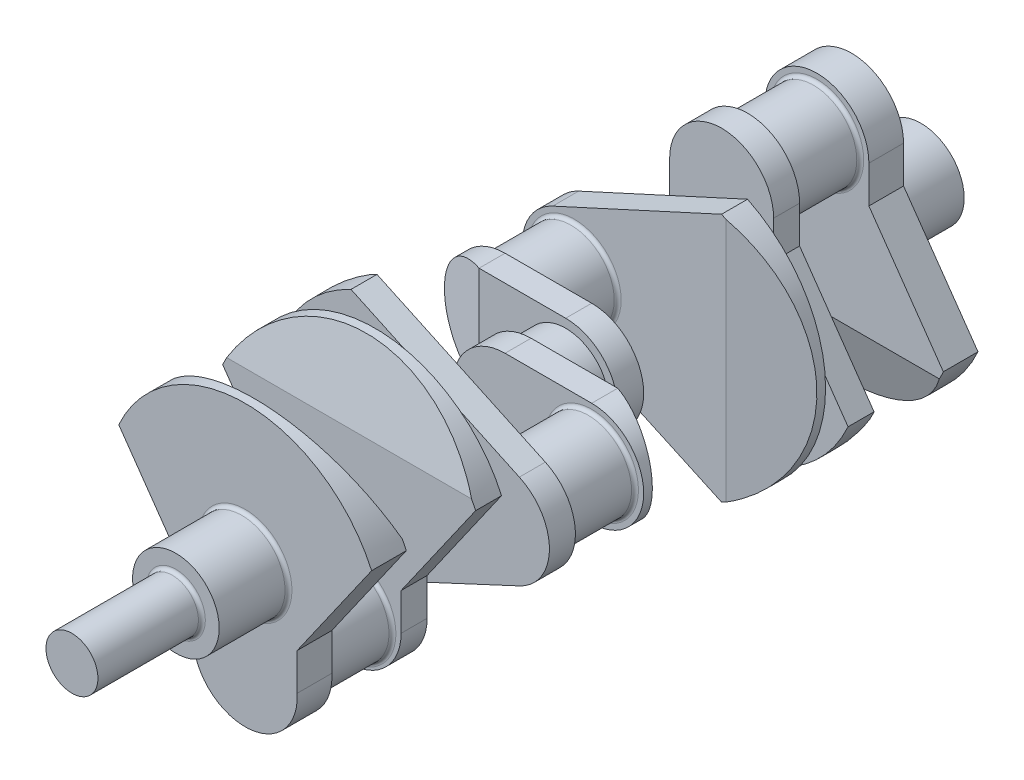
SolidWorks part; units mm, degrees
material "AISI 4340 Steel, normalized"
ref_plane "Front Plane" through (0, 0, 0) normal (0, 0, 1) x (1, 0, 0)
ref_plane "Top Plane" through (0, 0, 0) normal (0, 1, 0) x (1, 0, 0)
ref_plane "Right Plane" through (0, 0, 0) normal (1, 0, 0) x (0, 0, -1)
sketch "Sketch1" plane through (0, 0, 0) normal (0, 0, 1) x (1, 0, 0)
  circle A0 centre (0, 0) radius 31.75
  dimension "D1" = 63.5
extrude "Boss-Extrude1" add sketch "Sketch1" along normal blind 50.8
sketch "Sketch2" plane through (0, 0, 50.8) normal (0, 0, 1) x (1, 0, 0)
  line L0 (-38.1, 63.5) -> (-38.1, 36.322)
  line L1 (-38.1, 36.322) -> (-92.6807, -41.6274)
  line L2 (0, 115.8305) -> (0, -116.946) construction
  line L3 (38.1, 36.322) -> (92.6807, -41.6274)
  line L4 (38.1, 63.5) -> (38.1, 36.322)
  arc A0 (38.1, 63.5) -> (-38.1, 63.5) centre (0, 63.5) ccw
  arc A1 (-92.6807, -41.6274) -> (92.6807, -41.6274) centre (0, 0) ccw
  point P1 (38.1, 35.7985)
  point P3 (101.6, 0)
  point P13 (-92.7564, -41.4585)
  dimension "D1" = 203.2
  dimension "D3" = 38.1
  dimension "D2" = 63.5
  dimension "D4" = 27.178
  dimension "D5" = 145
extrude "Boss-Extrude2" add sketch "Sketch2" along normal blind 25.4
sketch "Sketch3" plane through (0, 0, 76.2) normal (0, 0, 1) x (1, 0, 0)
  circle A0 centre (0, 63.5) radius 31.75
  dimension "D1" = 63.5
extrude "Boss-Extrude3" add sketch "Sketch3" along normal blind 50.8
sketch "Sketch4" plane through (0, 0, 127) normal (0, 0, 1) x (1, 0, 0)
  line L0 (-38.1, 63.5) -> (-38.1, 36.322)
  line L1 (-38.1, 36.322) -> (-92.6807, -41.6274)
  line L2 (38.1, 63.5) -> (38.1, 36.322)
  line L3 (38.1, 36.322) -> (92.6807, -41.6274)
  line L4 (92.6807, -41.6274) -> (38.1, 36.322) construction
  arc A0 (38.1, 63.5) -> (-38.1, 63.5) centre (0, 63.5) ccw
  arc A1 (-92.6807, -41.6274) -> (92.6807, -41.6274) centre (0, 0) ccw
  point P1 (101.6, 0)
  point P4 (92.6807, -41.6274)
extrude "Boss-Extrude4" add sketch "Sketch4" along normal blind 19.05
sketch "Sketch5" plane through (0, 0, 146.05) normal (0, 0, 1) x (1, 0, 0)
  circle A0 centre (0, 0) radius 31.75
  dimension "D1" = 63.5
extrude "Boss-Extrude5" add sketch "Sketch5" along normal blind 25.4
sketch "Sketch6" plane through (0, 0, 171.45) normal (0, 0, 1) x (1, 0, 0)
  line L0 (-79.3697, 34.6761) -> (44.4018, 91.384)
  line L1 (44.4307, -91.37) -> (-79.322, -34.6209)
  arc A1 (-79.3697, 34.6761) -> (-79.322, -34.6209) centre (-63.5, 0.0385) ccw
  arc A2 (44.4307, -91.37) -> (44.4018, 91.384) centre (0, 0) ccw
  dimension "D1" = 63.5
  dimension "D2" = 38.1
  dimension "D3" = 101.6
  dimension "D4" = 136.144
extrude "Boss-Extrude6" add sketch "Sketch6" along normal blind 19.05
sketch "Sketch7" plane through (0, 0, 190.5) normal (0, 0, 1) x (1, 0, 0)
  circle A0 centre (-63.5, 0.0385) radius 31.75
  dimension "D1" = 63.5
extrude "Boss-Extrude7" add sketch "Sketch7" along normal blind 50.8
sketch "Sketch8" plane through (0, 0, 241.3) normal (0, 0, 1) x (1, 0, 0)
  line L0 (-63.5, 0) -> (0, 0) construction
  line L1 (-63.5, 38.1) -> (0, 38.1)
  line L2 (-63.5, -38.1) -> (0, -38.1)
  arc A0 (-63.5, 38.1) -> (-63.5, -38.1) centre (-63.5, 0) ccw
  arc A1 (0, -38.1) -> (0, 38.1) centre (0, 0) ccw
  point P4 (-31.75, 0)
  dimension "D1" = 38.1
extrude "Boss-Extrude8" add sketch "Sketch8" along normal blind 19.05
sketch "Sketch9" plane through (0, 0, 260.35) normal (0, 0, 1) x (1, 0, 0)
  circle A0 centre (0, 0) radius 31.75
  dimension "D1" = 63.5
extrude "Boss-Extrude9" add sketch "Sketch9" along normal blind 25.4
sketch "Sketch10" plane through (0, 0, 285.75) normal (0, 0, 1) x (1, 0, 0)
  line L0 (0, 0) -> (63.5, 0) construction
  line L1 (0, 38.1) -> (63.5, 38.1)
  line L2 (0, -38.1) -> (63.5, -38.1)
  arc A0 (0, 38.1) -> (0, -38.1) centre (0, 0) ccw
  arc A1 (63.5, -38.1) -> (63.5, 38.1) centre (63.5, 0) ccw
  point P4 (31.75, 0)
  dimension "D1" = 38.1
  dimension "D2" = 63.5
extrude "Boss-Extrude10" add sketch "Sketch10" along normal blind 19.05
sketch "Sketch11" plane through (0, 0, 304.8) normal (0, 0, 1) x (1, 0, 0)
  circle A0 centre (63.5, 0) radius 31.75
  dimension "D1" = 63.5
extrude "Boss-Extrude11" add sketch "Sketch11" along normal blind 50.8
sketch "Sketch12" plane through (0, 0, 355.6) normal (0, 0, 1) x (1, 0, 0)
  line L0 (-43.0921, 92.0088) -> (80.3275, 34.5391)
  line L1 (-43.0921, -92.0088) -> (80.3275, -34.5391)
  arc A0 (-43.0921, 92.0088) -> (-43.0921, -92.0088) centre (0, 0) ccw
  arc A1 (80.3275, -34.5391) -> (80.3275, 34.5391) centre (64.2446, 0) ccw
  point P1 (0, 101.6)
  point P4 (-50.2595, 88.298)
  point P7 (-37.9177, 94.2592)
  point P10 (3.2398, 101.462)
  point P12 (44.4307, -91.37)
  point P13 (-43.5194, -91.8075)
  point P14 (-7.4828, 96.0044)
  point P15 (3.2398, 101.462)
  point P16 (-43.0921, 92.0088)
  dimension "D1" = 38.1
  dimension "D3" = 101.6
  dimension "D2" = 136.144
extrude "Boss-Extrude12" add sketch "Sketch12" along normal blind 19.05
sketch "Sketch13" plane through (0, 0, 374.65) normal (0, 0, 1) x (1, 0, 0)
  circle A0 centre (0, 0) radius 31.75
  dimension "D1" = 63.5
extrude "Boss-Extrude13" add sketch "Sketch13" along normal blind 25.4
sketch "Sketch15" plane through (0, 0, 400.05) normal (0, 0, 1) x (1, 0, 0)
  line L0 (-38.1, -63.5) -> (-38.1, -36.322)
  line L1 (-38.1, -36.322) -> (-92.6807, 41.6274)
  line L2 (0, 94.3419) -> (0, -122.7433) construction
  line L3 (38.1, -63.5) -> (38.1, -36.322)
  line L4 (38.1, -36.322) -> (92.6807, 41.6274)
  arc A0 (-38.1, -63.5) -> (38.1, -63.5) centre (0, -63.5) ccw
  arc A2 (92.6807, 41.6274) -> (-92.6807, 41.6274) centre (0, 0) ccw
  point P1 (-38.1, -27.8487)
  point P3 (0, 0)
  point P13 (-63.5, 0)
  point P14 (-60.0415, -20.6704)
  point P15 (-60.0415, -20.6704)
  point P16 (-63.1756, 6.4107)
  dimension "D1" = 63.5
  dimension "D2" = 27.178
  dimension "D3" = 76.2
  dimension "D4" = 101.6
  dimension "D5" = 145
extrude "Boss-Extrude14" add sketch "Sketch15" along normal blind 19.05
sketch "Sketch16" plane through (0, 0, 419.1) normal (0, 0, 1) x (1, 0, 0)
  circle A0 centre (0, -65.6946) radius 31.75
  dimension "D1" = 63.5
extrude "Boss-Extrude15" add sketch "Sketch16" along normal blind 50.8
sketch "Sketch17" plane through (0, 0, 469.9) normal (0, 0, 1) x (1, 0, 0)
  line L0 (-92.6807, 41.6274) -> (-38.1, -36.322)
  line L1 (-38.1, -36.322) -> (-38.1, -63.5)
  line L2 (0, 109.8707) -> (0, -120.37) construction
  line L3 (38.1, -36.322) -> (38.1, -63.5)
  line L4 (92.6807, 41.6274) -> (38.1, -36.322)
  arc A2 (-38.1, -63.5) -> (38.1, -63.5) centre (0, -65.6946) ccw
  arc A3 (92.6807, 41.6274) -> (-92.6807, 41.6274) centre (0, 0) ccw
  point P1 (-101.6, 0)
  point P4 (-92.6807, 41.6274)
  dimension "D1" = 101.6
extrude "Boss-Extrude16" add sketch "Sketch17" along normal blind 25.4
sketch "Sketch18" plane through (0, 0, 495.3) normal (0, 0, 1) x (1, 0, 0)
  circle A0 centre (0, 0) radius 31.75
  dimension "D1" = 63.5
extrude "Boss-Extrude17" add sketch "Sketch18" along normal blind 50.8
sketch "Sketch19" plane through (0, 0, 546.1) normal (0, 0, 1) x (1, 0, 0)
  circle A0 centre (0, 0) radius 19.05
  dimension "D1" = 38.1
extrude "Boss-Extrude18" add sketch "Sketch19" along normal blind 76.2
fillet "Fillet1" radius 2.54 16 edges at (31.75, 0, 50.8) (31.75, 63.5, 127) (31.75, 0, 146.05) (31.75, 63.5, 76.2) (-31.75, 0.0385, 190.5) (31.75, 0, 171.45) (31.75, 0, 285.75) (-31.75, 0.0385, 241.3) (31.75, 0, 400.05) (95.25, 0, 304.8) (31.75, 0, 374.65) (95.25, 0, 355.6) (31.75, -65.6946, 419.1) (31.75, -65.6946, 469.9) (31.75, 0, 495.3) (19.05, 0, 546.1)
sketch "Sketch20" plane through (0, 0, 0) normal (1, 0, 0) x (0, 0, -1)
  line L0 (-488.95, 101.6) -> (-469.9, 47.625)
  line L1 (-469.9, 101.6) -> (-495.3, 101.6) construction
  line L2 (-469.9, 41.6274) -> (-469.9, 101.6) construction
  line L3 (-469.9, 47.625) -> (-469.9, 101.6)
  line L4 (-469.9, 101.6) -> (-488.95, 101.6)
  line L5 (-419.1, 47.625) -> (-419.1, 101.6)
  line L6 (-419.1, 101.6) -> (-419.1, 41.6274) construction
  line L7 (-419.1, 101.6) -> (-406.4, 101.6)
  line L8 (-400.05, 101.6) -> (-419.1, 101.6) construction
  line L9 (-406.4, 101.6) -> (-419.1, 47.625)
  line L10 (-139.7, -101.6) -> (-127, -101.6)
  line L11 (-146.05, -101.6) -> (-127, -101.6) construction
  line L12 (-127, -101.6) -> (-127, -47.625)
  line L13 (-127, -101.6) -> (-127, -41.6274) construction
  line L14 (-127, -47.625) -> (-139.7, -101.6)
  line L15 (-57.15, -101.6) -> (-76.2, -101.6)
  line L16 (-76.2, -101.6) -> (-76.2, -47.625)
  line L17 (-76.2, -41.6274) -> (-76.2, -101.6) construction
  line L18 (-76.2, -47.625) -> (-57.15, -101.6)
  dimension "D1" = 19.05
  dimension "D2" = 12.7
  dimension "D3" = 53.975
  dimension "D4" = 53.975
  dimension "D5" = 53.975
  dimension "D6" = 12.7
  dimension "D7" = 19.05
  dimension "D8" = 53.975
extrude "Cut-Extrude1" cut sketch "Sketch20" against normal mid plane 277.114
sketch "Sketch21" plane through (0, 0, 0) normal (0, 1, 0) x (1, 0, 0)
  line L0 (101.6, -177.8) -> (101.6, -190.5)
  line L1 (101.6, -190.5) -> (101.6, -171.45) construction
  line L2 (101.6, -190.5) -> (47.625, -190.5)
  line L3 (44.4018, -190.5) -> (101.6, -190.5) construction
  line L4 (47.625, -190.5) -> (101.6, -177.8)
  line L5 (-101.6, -247.65) -> (-101.6, -260.35)
  line L6 (-101.6, -241.3) -> (-101.6, -260.35) construction
  line L7 (-101.6, -260.35) -> (-63.5, -260.35)
  line L8 (0, -260.35) -> (-63.5, -260.35) construction
  line L9 (-63.5, -260.35) -> (-101.6, -247.65)
  line L10 (63.5, -285.75) -> (101.6, -285.75)
  line L11 (101.6, -285.75) -> (63.5, -285.75) construction
  line L12 (101.6, -285.75) -> (101.6, -298.45)
  line L13 (101.6, -304.8) -> (101.6, -285.75) construction
  line L14 (101.6, -298.45) -> (63.5, -285.75)
  line L15 (63.5, -304.8) -> (63.5, -285.75) construction
  line L16 (-101.6, -355.6) -> (-101.6, -368.3)
  line L17 (-101.6, -355.6) -> (-101.6, -374.65) construction
  line L18 (-101.6, -368.3) -> (-47.625, -355.6)
  line L19 (-43.0921, -355.6) -> (-101.6, -355.6) construction
  line L20 (-47.625, -355.6) -> (-101.6, -355.6)
  dimension "D1" = 53.975
  dimension "D2" = 12.7
  dimension "D3" = 12.7
  dimension "D4" = 12.7
  dimension "D5" = 53.975
  dimension "D6" = 12.7
extrude "Cut-Extrude2" cut sketch "Sketch21" against normal mid plane 284.48
